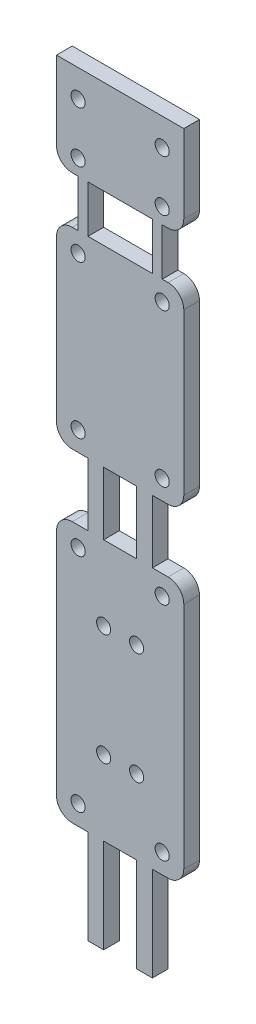
SolidWorks part; units mm, degrees
ref_plane "Front Plane" through (0, 0, 0) normal (0, 0, 1) x (1, 0, 0)
ref_plane "Top Plane" through (0, 0, 0) normal (0, 1, 0) x (1, 0, 0)
ref_plane "Right Plane" through (0, 0, 0) normal (1, 0, 0) x (0, 0, -1)
sketch "Sketch1" plane through (0, 0, 0) normal (0, 0, 1) x (1, 0, 0)
  line L0 (16.2, 1.5) -> (16.2, 14) construction
  line L1 (16.2, 109.64) -> (0, 109.64)
  line L2 (0, 109.64) -> (0, 99.66)
  line L3 (0, 1.5) -> (16.2, 1.5) construction
  line L4 (14.2, 59.21) -> (12.2, 59.21)
  line L5 (0, 14) -> (4, 14) construction
  line L6 (2, 26) -> (4, 26)
  line L7 (2, 91.66) -> (2.75, 91.66)
  line L8 (2, 67.21) -> (4, 67.21)
  line L9 (8.1, 109.64) -> (8.1, 97.66) construction
  line L10 (0, 14) -> (0, 1.5) construction
  line L11 (2, 97.66) -> (2.75, 97.66)
  line L12 (16.2, 28) -> (16.2, 57.21)
  line L13 (16.2, 99.66) -> (16.2, 109.64)
  line L14 (0, 89.66) -> (0, 69.21)
  line L15 (0, 57.21) -> (0, 28)
  line L16 (16.2, 69.21) -> (16.2, 89.66)
  line L17 (6, 14) -> (6, 26)
  line L18 (4, 59.21) -> (4, 67.21)
  line L19 (4, 14) -> (4, 26)
  line L20 (6, 59.21) -> (6, 67.21)
  line L21 (4, 91.66) -> (4, 97.66)
  line L22 (2.75, 97.66) -> (2.75, 91.66)
  line L23 (10.2, 14) -> (10.2, 26)
  line L24 (12.2, 14) -> (12.2, 26)
  line L25 (10.2, 59.21) -> (10.2, 67.21)
  line L26 (12.2, 59.21) -> (12.2, 67.21)
  line L27 (13.45, 91.66) -> (13.45, 97.66)
  line L28 (12.2, 91.66) -> (12.2, 97.66)
  line L29 (4, 97.66) -> (12.2, 97.66)
  line L30 (4, 91.66) -> (12.2, 91.66)
  line L31 (13.45, 91.66) -> (14.2, 91.66)
  line L32 (13.45, 97.66) -> (14.2, 97.66)
  line L33 (6, 67.21) -> (10.2, 67.21)
  line L34 (12.2, 67.21) -> (14.2, 67.21)
  line L35 (10.2, 59.21) -> (6, 59.21)
  line L36 (4, 59.21) -> (2, 59.21)
  line L37 (6, 14) -> (10.2, 14) construction
  line L38 (6, 26) -> (10.2, 26)
  line L39 (12.2, 26) -> (14.2, 26)
  line L40 (12.2, 14) -> (16.2, 14) construction
  line L41 (12.2, 14) -> (10.2, 14)
  line L42 (6, 14) -> (4, 14)
  circle A0 centre (13.45, 56.71) radius 0.9
  circle A1 centre (10.2, 49.71) radius 0.9
  circle A2 centre (13.45, 106.16) radius 0.9
  circle A3 centre (2.75, 99.66) radius 0.9
  circle A4 centre (6, 49.71) radius 0.9
  circle A5 centre (2.75, 28.5) radius 0.9
  circle A6 centre (2.75, 89.16) radius 0.9
  circle A7 centre (2.75, 56.71) radius 0.9
  circle A8 centre (13.45, 89.16) radius 0.9
  circle A9 centre (13.45, 99.66) radius 0.9
  arc A10 (16.2, 28) -> (14.2, 26) centre (14.2, 28) cw
  arc A11 (0, 28) -> (2, 26) centre (2, 28) ccw
  arc A12 (16.2, 57.21) -> (14.2, 59.21) centre (14.2, 57.21) ccw
  arc A13 (0, 57.21) -> (2, 59.21) centre (2, 57.21) cw
  arc A14 (16.2, 69.21) -> (14.2, 67.21) centre (14.2, 69.21) cw
  arc A15 (0, 69.21) -> (2, 67.21) centre (2, 69.21) ccw
  arc A16 (0, 89.66) -> (2, 91.66) centre (2, 89.66) cw
  arc A17 (16.2, 89.66) -> (14.2, 91.66) centre (14.2, 89.66) ccw
  arc A18 (16.2, 99.66) -> (14.2, 97.66) centre (14.2, 99.66) cw
  arc A19 (2, 97.66) -> (0, 99.66) centre (2, 99.66) cw
  circle A28 centre (13.45, 69.71) radius 0.9
  circle A29 centre (6, 35.5) radius 0.9
  circle A32 centre (2.75, 106.16) radius 0.9
  circle A33 centre (10.2, 35.5) radius 0.9
  circle A34 centre (2.75, 69.71) radius 0.9
  circle A35 centre (13.45, 28.5) radius 0.9
  circle A36 centre (2.85, 11.5) radius 0.9 construction
  circle A37 centre (13.35, 11.5) radius 0.9 construction
  circle A38 centre (13.35, 5.5) radius 0.9 construction
  circle A39 centre (2.85, 5.5) radius 0.9 construction
  point P71 (16.2, 26)
  point P74 (0, 26)
  point P91 (16.2, 59.21)
  point P94 (0, 59.21)
  point P97 (16.2, 67.21)
  point P100 (0, 67.21)
  point P103 (0, 91.66)
  point P106 (16.2, 91.66)
  point P109 (16.2, 97.66)
  point P112 (0, 97.66)
  dimension "D1" = 4
  dimension "D45" = 1.8
  dimension "D46" = 2
  dimension "D2" = 4
  dimension "D3" = 2.85
  dimension "D4" = 2.85
  dimension "D5" = 16.2
  dimension "D6" = 6
  dimension "D7" = 6
  dimension "D8" = 2.85
  dimension "D9" = 2.85
  dimension "D10" = 2.5
  dimension "D11" = 12
  dimension "D12" = 33.21
  dimension "D13" = 2.5
  dimension "D14" = 2.5
  dimension "D15" = 2.75
  dimension "D16" = 2.75
  dimension "D17" = 2.5
  dimension "D18" = 2.5
  dimension "D19" = 2.75
  dimension "D20" = 2.75
  dimension "D21" = 9.5
  dimension "D22" = 6
  dimension "D23" = 9.5
  dimension "D24" = 6
  dimension "D25" = 9.5
  dimension "D26" = 9.5
  dimension "D27" = 6
  dimension "D28" = 6
  dimension "D29" = 8
  dimension "D30" = 24.45
  dimension "D31" = 2.5
  dimension "D32" = 2.5
  dimension "D33" = 2.75
  dimension "D34" = 2.75
  dimension "D35" = 6
  dimension "D36" = 2.75
  dimension "D37" = 2
  dimension "D38" = 2.75
  dimension "D39" = 8.5
  dimension "D40" = 11.98
  dimension "D41" = 2.5
  dimension "D42" = 2.5
  dimension "D43" = 2.75
  dimension "D44" = 2.75
extrude "Boss-Extrude1" add sketch "Sketch1" along normal blind 2
sketch "Sketch2" plane through (0, 0, 0) normal (0, 0, -1) x (-1, 0, 0)
  line L0 (-13.45, 97.66) -> (-2.75, 97.66)
  line L1 (-2.75, 97.66) -> (-2.75, 91.66)
  line L2 (-2.75, 91.66) -> (-13.45, 91.66)
  line L3 (-13.45, 91.66) -> (-13.45, 97.66)
  line L4 (-12.2, 67.21) -> (-4, 67.21)
  line L5 (-4, 67.21) -> (-4, 59.21)
  line L6 (-4, 59.21) -> (-12.2, 59.21)
  line L7 (-12.2, 59.21) -> (-12.2, 67.21)
  line L8 (-12.2, 26) -> (-4, 26)
  line L9 (-4, 26) -> (-4, 14)
  line L10 (-4, 14) -> (-12.2, 14)
  line L11 (-12.2, 14) -> (-12.2, 26)
extrude "Cut-Extrude1" [suppressed] cut sketch "Sketch2" against normal up to surface (2 mm away)
equation "\"D12@Sketch1\"= \"HL@parametersSketch@prostheticParameters.SLDPRT\" * 0.266 - 12 - 4 'Middle PIP Length"
equation "\"D30@Sketch1\"= \"HL@parametersSketch@prostheticParameters.SLDPRT\" * 0.17 - 4 - 3'Middle MIP Length"
equation "\"D5@Sketch1\"= \"fingerWidth@parametersSketch@prostheticParameters.SLDPRT\" 'Middle Width"
equation "\"D40@Sketch1\"= \"HL@parametersSketch@prostheticParameters.SLDPRT\" * 0.108 - 3 - 5'Middle DIP Length"
equation "\"D45@Sketch1\"= 1.5 + \"tol1@parametersSketch@prostheticParameters.SLDPRT\""
